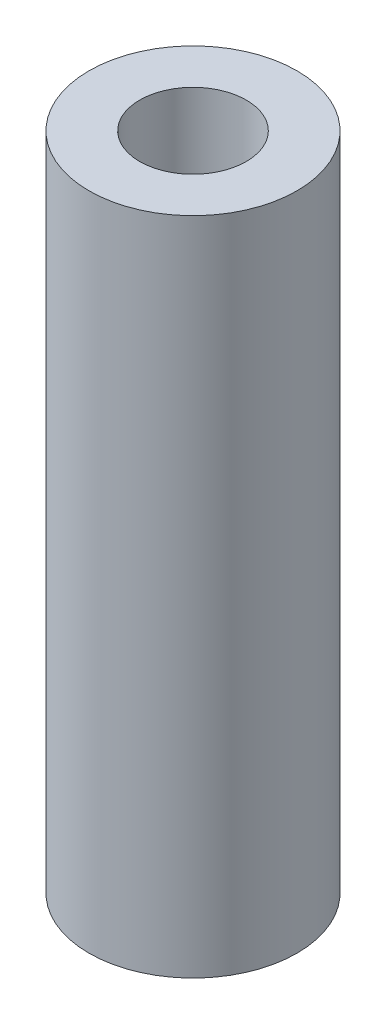
SolidWorks part; units mm, degrees
ref_plane "Front Plane" through (0, 0, 0) normal (0, 0, 1) x (1, 0, 0)
ref_plane "Top Plane" through (0, 0, 0) normal (0, 1, 0) x (1, 0, 0)
ref_plane "Right Plane" through (0, 0, 0) normal (1, 0, 0) x (0, 0, -1)
sketch "Sketch1" plane through (0, 0, 0) normal (0, 1, 0) x (1, 0, 0)
  circle A0 centre (0, 0) radius 4
  dimension "D1" = 8
extrude "Boss-Extrude1" add sketch "Sketch1" along normal blind 25.4
sketch "Sketch2" plane through (0, 25.4, 0) normal (0, 1, 0) x (1, 0, 0)
  circle A0 centre (0, 0) radius 2.05
  dimension "D1" = 4.1
extrude "Cut-Extrude1" cut sketch "Sketch2" against normal through all
